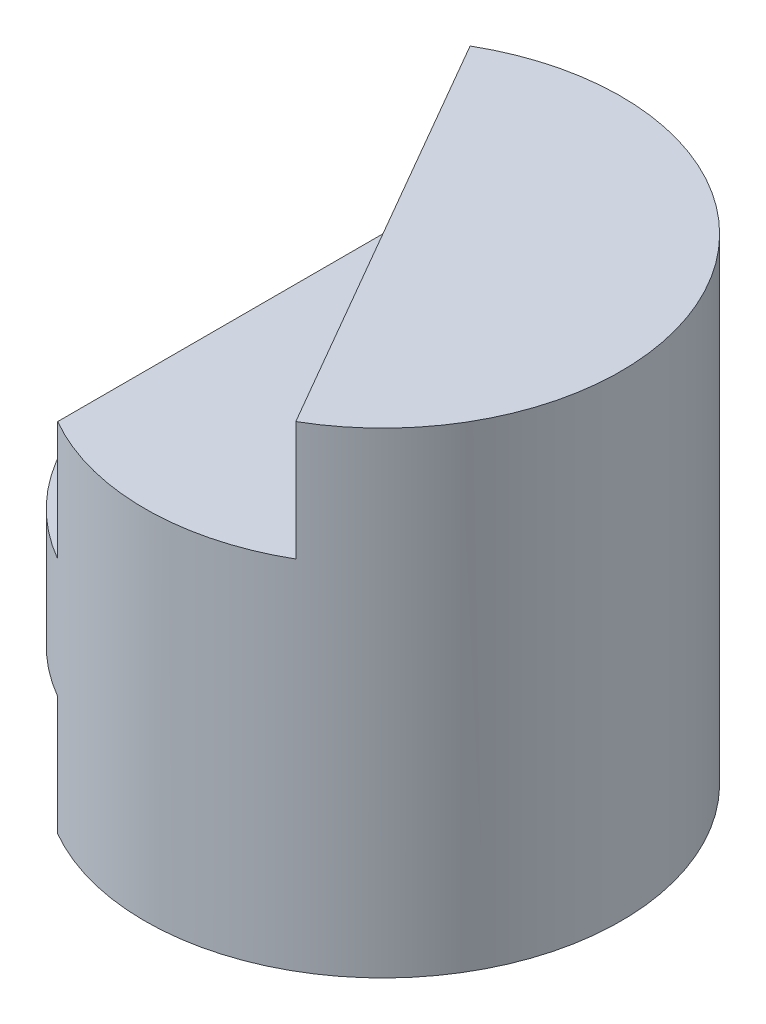
SolidWorks part; units mm, degrees
ref_plane "Front" through (0, 0, 0) normal (0, 0, 1) x (1, 0, 0)
ref_plane "Top" through (0, 0, 0) normal (0, 1, 0) x (1, 0, 0)
ref_plane "Right" through (0, 0, 0) normal (1, 0, 0) x (0, 0, -1)
sketch "Sketch1" plane through (0, 0, 0) normal (0, 1, 0) x (1, 0, 0)
  circle A0 centre (0, 0) radius 2
  dimension "D1" = 4
extrude "Boss-Extrude1" add sketch "Sketch1" along normal blind 4
sketch "Sketch2" plane through (0, 0, 0) normal (0, 0, 1) x (1, 0, 0)
  line L0 (-1, 4) -> (-1, 2)
  line L1 (2, 4) -> (-2, 4) construction
  line L2 (-2, 4) -> (-2, 0) construction
  line L3 (-2, 0) -> (2, 0) construction
  line L4 (-1, 2) -> (-2, 2)
  line L6 (-1, 1) -> (-2, 1)
  line L8 (-2, 0) -> (-2, 1)
  line L9 (-2, 4) -> (-1, 4)
  line L10 (-1, 0) -> (-2, 0)
  line L11 (-1, 1) -> (-1, 0)
  line L12 (-2, 2) -> (-2, 4)
  dimension "D1" = 1
  dimension "D2" = 1
  dimension "D3" = 1
extrude "Cut-Extrude1" cut sketch "Sketch2" against normal mid plane 4
sketch "Sketch3" plane through (0, 4, 0) normal (0, 1, 0) x (1, 0, 0)
  line L1 (1, -1.7321) -> (-1, 1.7321)
  line L2 (1, -1.7321) -> (2.1949, -3.0912)
  line L3 (2.1949, -3.0912) -> (-1.9972, -4.109)
  line L4 (-1.9972, -4.109) -> (-1, -1.7321)
  arc A0 (-1, -1.7321) -> (-1, 1.7321) centre (0, 0) ccw construction
extrude "Cut-Extrude4" cut sketch "Sketch3" against normal blind 1 and the other way through all
